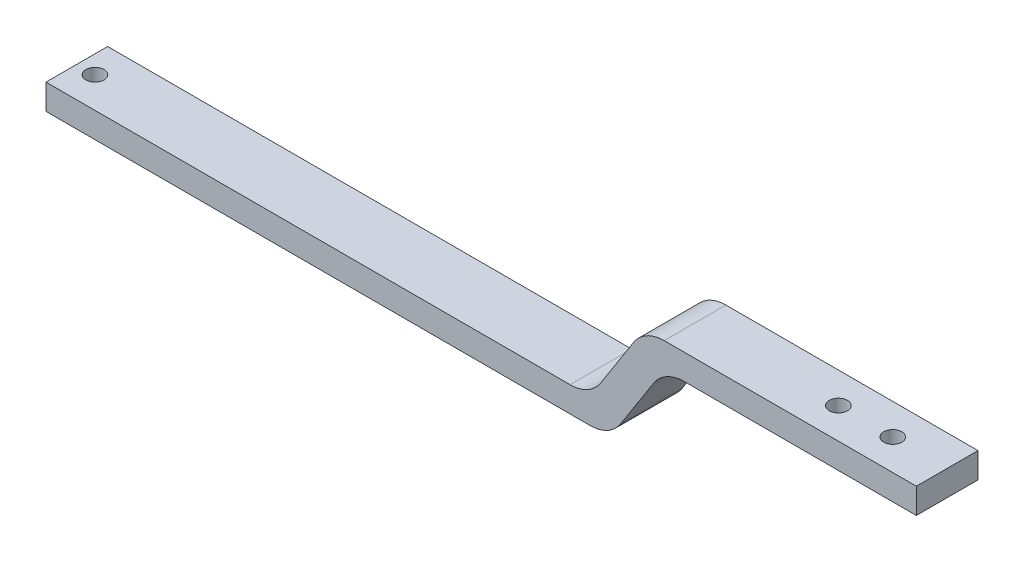
SolidWorks part; units mm, degrees
ref_plane "Front Plane" through (0, 0, 0) normal (0, 0, 1) x (1, 0, 0)
ref_plane "Top Plane" through (0, 0, 0) normal (0, 1, 0) x (1, 0, 0)
ref_plane "Right Plane" through (0, 0, 0) normal (1, 0, 0) x (0, 0, -1)
sketch "Sketch1" plane through (0, 0, 0) normal (0, 0, 1) x (1, 0, 0)
  line L0 (-145.7371, 14.8242) -> (4.2629, 14.8242)
  line L1 (4.2629, 14.8242) -> (19.2629, 38.3242)
  line L2 (19.2629, 38.3242) -> (94.2629, 38.3242)
  line L3 (94.2629, 38.3242) -> (94.2629, 31.3242)
  line L4 (94.2629, 31.3242) -> (24.7691, 31.3242)
  line L5 (24.7691, 31.3242) -> (9.7691, 7.8242)
  line L6 (9.7691, 7.8242) -> (-145.7371, 7.8242)
  line L7 (-145.7371, 7.8242) -> (-145.7371, 14.8242)
  dimension "D1" = 150
  dimension "D2" = 15
  dimension "D3" = 23.5
  dimension "D4" = 75
  dimension "D5" = 7
  dimension "D6" = 7
extrude "Extrude1" add sketch "Sketch1" along normal blind 17
fillet "Fillet1" radius 10 4 edges at (24.7691, 31.3242, 8.5) (9.7691, 7.8242, 8.5) (19.2629, 38.3242, 8.5) (4.2629, 14.8242, 8.5)
sketch "Sketch2" plane through (0, 38.3242, 0) normal (0, 1, 0) x (1, 0, 0)
  line L0 (94.2629, -17) -> (94.2629, 0) construction
  circle A0 centre (79.2629, -8.5) radius 2.5
  circle A1 centre (64.2629, -8.5) radius 2.5
  dimension "D1" = 5
  dimension "D2" = 5
  dimension "D3" = 15
  dimension "D4" = 15
extrude "Extrude2" cut sketch "Sketch2" against normal blind 17
sketch "Sketch3" plane through (0, 7.8242, 0) normal (0, -1, 0) x (1, 0, 0)
  line L0 (-145.7371, 17) -> (4.2886, 17) construction
  line L2 (-145.7371, 17) -> (-145.7371, 0) construction
  circle A0 centre (-140.7371, 8.5) radius 2.5
  dimension "D1" = 5
  dimension "D2" = 8.5
  dimension "D3" = 5
extrude "Extrude3" cut sketch "Sketch3" against normal blind 17
